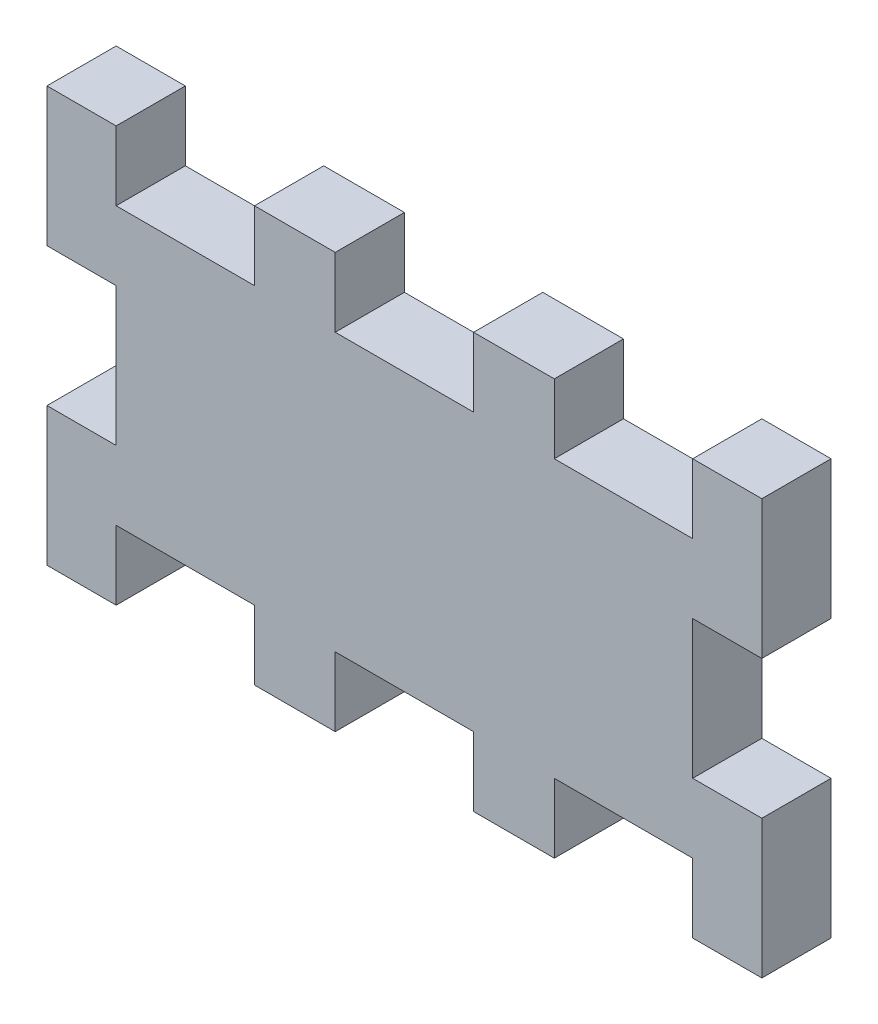
SolidWorks part; units mm, degrees
ref_plane "Front Plane" through (0, 0, 0) normal (0, 0, 1) x (1, 0, 0)
ref_plane "Top Plane" through (0, 0, 0) normal (0, 1, 0) x (1, 0, 0)
ref_plane "Right Plane" through (0, 0, 0) normal (1, 0, 0) x (0, 0, -1)
sketch "Sketch3" plane through (0, 0, 0) normal (0, 0, 1) x (1, 0, 0)
  line L0 (-19.527, 0) -> (20.4279, 0) construction
  line L1 (0, 13.2545) -> (0, -13.75) construction
  line L2 (-15.5, 3) -> (-15.5, 9)
  line L3 (-12.5, 6) -> (-6.5, 6)
  line L4 (-12.5, 3) -> (-12.5, -3)
  line L5 (-12.5, -6) -> (-6.5, -6)
  line L6 (12.5, 3) -> (12.5, -3)
  line L8 (-3, -6) -> (-3, -9)
  line L9 (-3, -9) -> (-6.5, -9)
  line L10 (-6.5, -6) -> (-6.5, -9)
  line L11 (-12.5, -3) -> (-15.5, -3)
  line L12 (-12.5, -6) -> (-12.5, -9)
  line L13 (-12.5, -9) -> (-15.5, -9)
  line L14 (-15.5, -3) -> (-15.5, -9)
  line L15 (-12.5, 9) -> (-15.5, 9)
  line L16 (-12.5, 6) -> (-12.5, 9)
  line L17 (-12.5, 3) -> (-15.5, 3)
  line L18 (12.5, 3) -> (15.5, 3)
  line L19 (12.5, 6) -> (12.5, 9)
  line L20 (12.5, 9) -> (15.5, 9)
  line L21 (15.5, -3) -> (15.5, -9)
  line L22 (12.5, -9) -> (15.5, -9)
  line L23 (12.5, -6) -> (12.5, -9)
  line L24 (12.5, -3) -> (15.5, -3)
  line L25 (15.5, 3) -> (15.5, 9)
  line L26 (6.5, -6) -> (6.5, -9)
  line L27 (3, -9) -> (6.5, -9)
  line L28 (3, -6) -> (3, -9)
  line L31 (3, 6) -> (3, 9)
  line L32 (3, 9) -> (6.5, 9)
  line L33 (6.5, 6) -> (6.5, 9)
  line L34 (-6.5, 6) -> (-6.5, 9)
  line L35 (-3, 9) -> (-6.5, 9)
  line L36 (-3, 6) -> (-3, 9)
  line L38 (-3, 6) -> (3, 6)
  line L39 (6.5, 6) -> (12.5, 6)
  line L40 (6.5, -6) -> (12.5, -6)
  line L41 (-3, -6) -> (3, -6)
  point P17 (-14, -9)
  dimension "D2" = 12.5
  dimension "D3" = 6
  dimension "D4" = 12.5
  dimension "D5" = 3
  dimension "D6" = 3.5
  dimension "D7" = 3
  dimension "D8" = 3
  dimension "D9" = 3
  dimension "D10" = 6
extrude "Boss-Extrude1" add sketch "Sketch3" along normal blind 3
